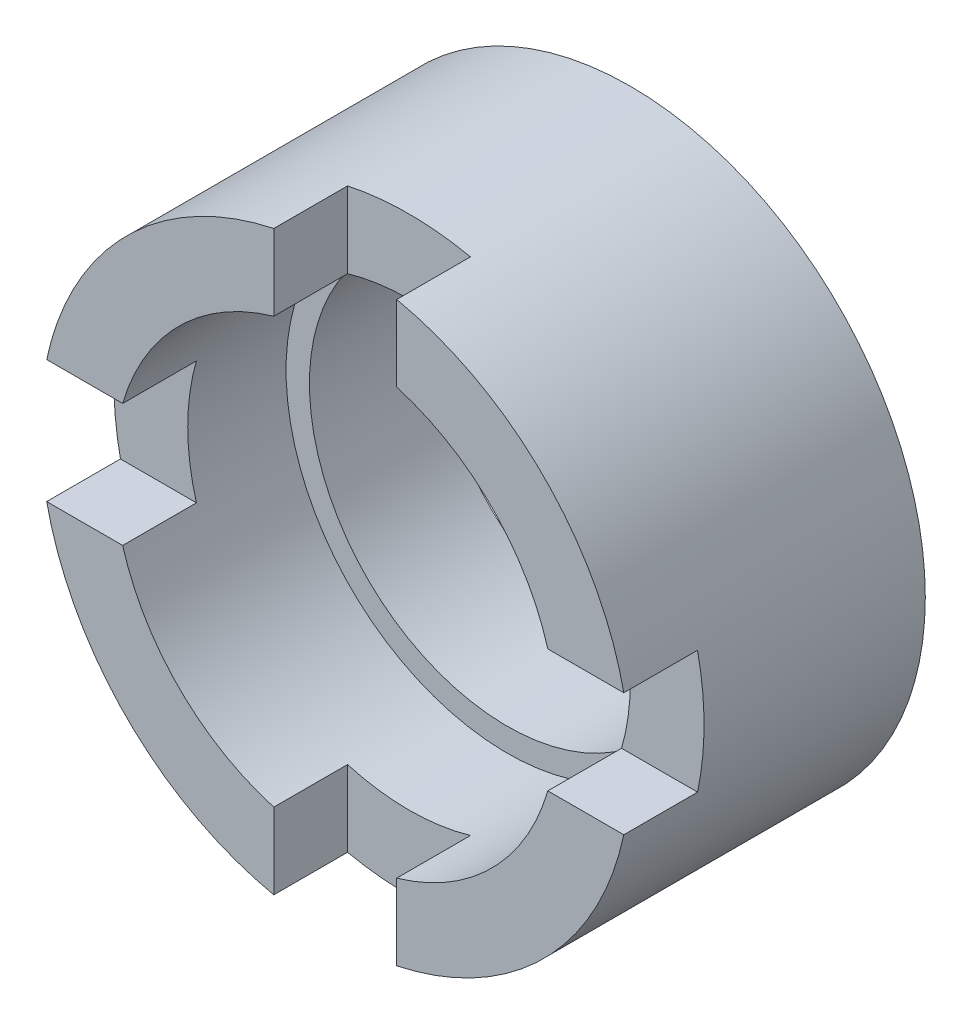
SolidWorks part; units mm, degrees
ref_plane "前视基准面" through (0, 0, 0) normal (0, 0, 1) x (1, 0, 0)
ref_plane "上视基准面" through (0, 0, 0) normal (0, 1, 0) x (1, 0, 0)
ref_plane "右视基准面" through (0, 0, 0) normal (1, 0, 0) x (0, 0, -1)
sketch "草图1" plane through (0, 0, 0) normal (0, 0, 1) x (1, 0, 0)
  circle A0 centre (0, 0) radius 8.05
  circle A1 centre (0, 0) radius 12
  dimension "D1" = 16.1
  dimension "D2" = 24
extrude "凸台-拉伸1" add sketch "草图1" along normal blind 12
sketch "草图3" plane through (0, 0, 12) normal (0, 0, 1) x (1, 0, 0)
  line L0 (-18.1676, 0) -> (19.0269, 0) construction
  line L1 (-16.5, 2.5) -> (-2.5, 2.5)
  line L2 (-16.5, 2.5) -> (-16.5, -2.5)
  line L3 (-16.5, -2.5) -> (-2.5, -2.5)
  line L4 (16.5, 2.5) -> (16.5, -2.5)
  line L5 (-2.5, 16.5) -> (2.5, 16.5)
  line L6 (-2.5, 16.5) -> (-2.5, 2.5)
  line L7 (-2.5, -16.5) -> (2.5, -16.5)
  line L8 (2.5, 16.5) -> (2.5, 2.5)
  line L9 (0, 13.161) -> (0, -13.4065) construction
  line L10 (2.5, 2.5) -> (16.5, 2.5)
  line L11 (-2.5, -2.5) -> (-2.5, -16.5)
  line L12 (2.5, -2.5) -> (16.5, -2.5)
  line L13 (2.5, -2.5) -> (2.5, -16.5)
  dimension "D1" = 5
  dimension "D2" = 14
  dimension "D3" = 14
extrude "切除-拉伸1" cut sketch "草图3" against normal blind 3
sketch "草图4" plane through (0, 0, 12) normal (0, 0, 1) x (1, 0, 0)
  circle A0 centre (0, 0) radius 9
  dimension "D1" = 18
extrude "切除-拉伸2" cut sketch "草图4" against normal blind 7
